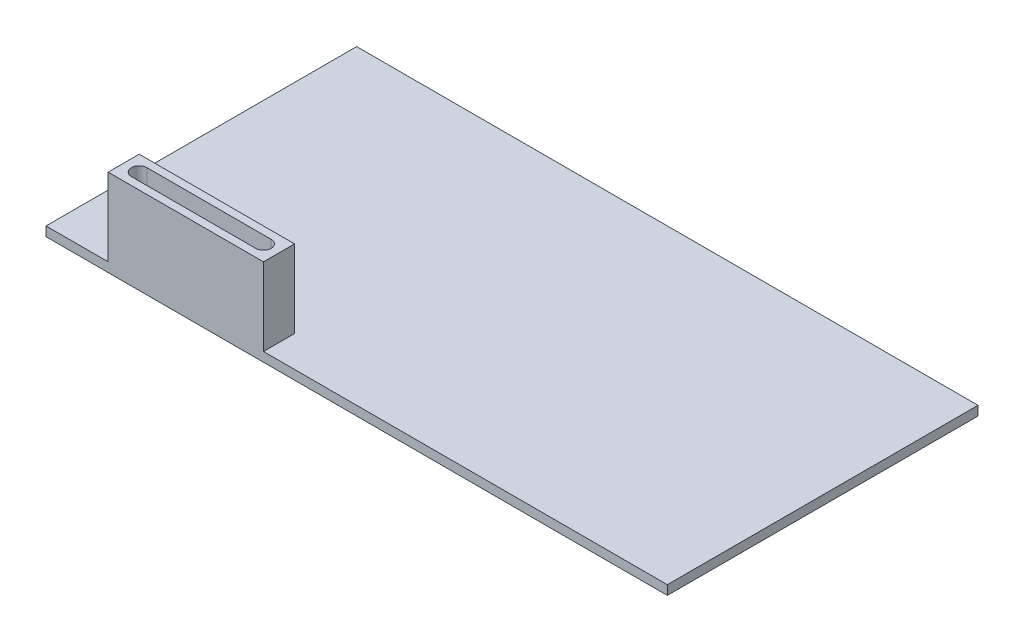
SolidWorks part; units mm, degrees
ref_plane "Front Plane" through (0, 0, 0) normal (0, 0, 1) x (1, 0, 0)
ref_plane "Top Plane" through (0, 0, 0) normal (0, 1, 0) x (1, 0, 0)
ref_plane "Right Plane" through (0, 0, 0) normal (1, 0, 0) x (0, 0, -1)
sketch "Sketch1" plane through (0, 0, 0) normal (0, 1, 0) x (1, 0, 0)
  line L1 (-100, 50) -> (100, 50)
  line L2 (-100, 50) -> (-100, -50)
  line L3 (-100, -50) -> (100, -50)
  line L4 (100, 50) -> (100, -50)
  line L5 (0, -50) -> (0, 50) construction
  line L6 (-100, 0) -> (100, 0) construction
  point P0 (0, 0)
  dimension "D1" = 200
  dimension "D2" = 100
extrude "Boss-Extrude1" add sketch "Sketch1" along normal blind 3
sketch "Sketch2" plane through (0, 3, 0) normal (0, 1, 0) x (1, 0, 0)
  line L0 (-100, -50) -> (100, -50) construction
  line L1 (-80, -50) -> (-30, -50)
  line L2 (-80, -50) -> (-80, -40)
  line L3 (-80, -40) -> (-30, -40)
  line L4 (-30, -50) -> (-30, -40)
  line L5 (-55, -40) -> (-55, -50) construction
  line L6 (-80, -45) -> (-30, -45) construction
  line L7 (-100, 50) -> (-100, -50) construction
  point P104 (-55, -45)
  dimension "D1" = 10
  dimension "D2" = 50
  dimension "D3" = 20
extrude "Boss-Extrude2" add sketch "Sketch2" along normal blind 25
sketch "Sketch3" plane through (0, 28, 0) normal (0, 1, 0) x (1, 0, 0)
  line L0 (-80, -45) -> (-30, -45) construction
  line L1 (-80, -40) -> (-80, -50) construction
  line L2 (-30, -50) -> (-30, -40) construction
  line L3 (-75, -45) -> (-35, -45) construction
  line L4 (-75, -42.5) -> (-35, -42.5)
  line L5 (-75, -47.5) -> (-35, -47.5)
  arc A0 (-75, -42.5) -> (-75, -47.5) centre (-75, -45) ccw
  arc A1 (-35, -47.5) -> (-35, -42.5) centre (-35, -45) ccw
  point P8 (-55, -45)
  dimension "D2" = 40
  dimension "D1" = 5
extrude "Cut-Extrude1" cut sketch "Sketch3" against normal through all
